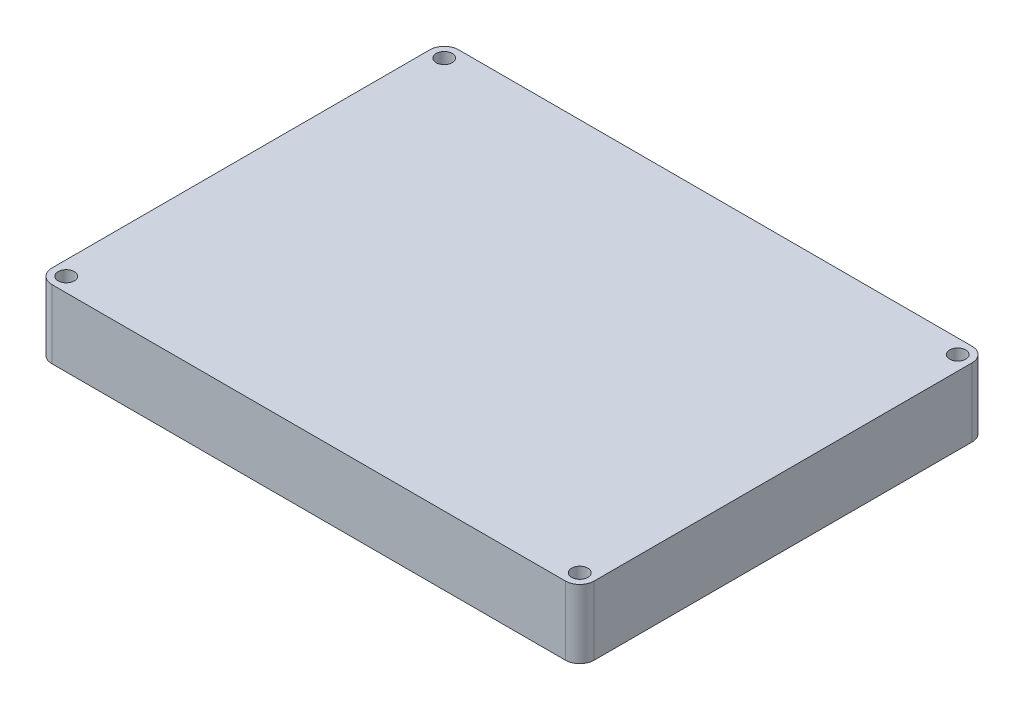
SolidWorks part; units mm, degrees
ref_plane "Front Plane" through (0, 0, 0) normal (0, 0, 1) x (1, 0, 0)
ref_plane "Top Plane" through (0, 0, 0) normal (0, 1, 0) x (1, 0, 0)
ref_plane "Right Plane" through (0, 0, 0) normal (1, 0, 0) x (0, 0, -1)
sketch "Sketch1" plane through (0, 205.1811, 0) normal (0, 1, 0) x (1, 0, 0)
  line L0 (160.5069, -319.0795) -> (160.5069, -311.1795) construction
  line L1 (43.6819, -244.0795) -> (157.3319, -244.0795)
  line L2 (40.5069, -247.2545) -> (40.5069, -330.9045)
  line L3 (43.6819, -334.0795) -> (157.3319, -334.0795)
  line L4 (160.5069, -247.2545) -> (160.5069, -330.9045)
  line L7 (157.5069, -244.0795) -> (48.5069, -244.0795) construction
  arc A0 (157.3319, -244.0795) -> (160.5069, -247.2545) centre (157.3319, -247.2545) cw
  arc A1 (157.3319, -334.0795) -> (160.5069, -330.9045) centre (157.3319, -330.9045) ccw
  arc A2 (40.5069, -330.9045) -> (43.6819, -334.0795) centre (43.6819, -330.9045) ccw
  arc A3 (40.5069, -247.2545) -> (43.6819, -244.0795) centre (43.6819, -247.2545) cw
  dimension "D1" = 3.175
  dimension "D2" = 120
  dimension "D3" = 90
extrude "Boss-Extrude1" add sketch "Sketch1" along normal up to surface (15.18 mm away) from surface at -5.98
hole_wizard "9/64 (0.14063) Diameter Hole1" positions "Sketch2" profile "Sketch3" hole size "9/64" standard "ANSI Inch" end condition through all
sketch "Sketch2" plane through (0, 214.3811, 0) normal (0, 1, 0) x (1, 0, 0)
  arc A4 (43.6819, -244.0795) -> (40.5069, -247.2545) centre (43.6819, -247.2545) ccw construction
  arc A5 (160.5069, -247.2545) -> (157.3319, -244.0795) centre (157.3319, -247.2545) ccw construction
  point P0 (43.6819, -330.9045)
  point P2 (43.6819, -247.2545)
  point P4 (157.3319, -247.2545)
  point P6 (157.3319, -330.9045)
sketch "Sketch3" plane through (43.6819, 214.3811, 330.9045) normal (1, 0, 0) x (0, 0, 1)
  line L0 (0, 0) -> (0, 15.18)
  line L1 (0, 15.18) -> (1.786, 15.18)
  line L2 (1.786, 15.18) -> (1.786, 0)
  line L5 (1.786, 0) -> (0, 0)
  line L11 (0, -6.35) -> (0, 107.95) construction
  dimension "Thru Hole Dia." = 3.572
  dimension "Thru Hole Depth" = 15.18
